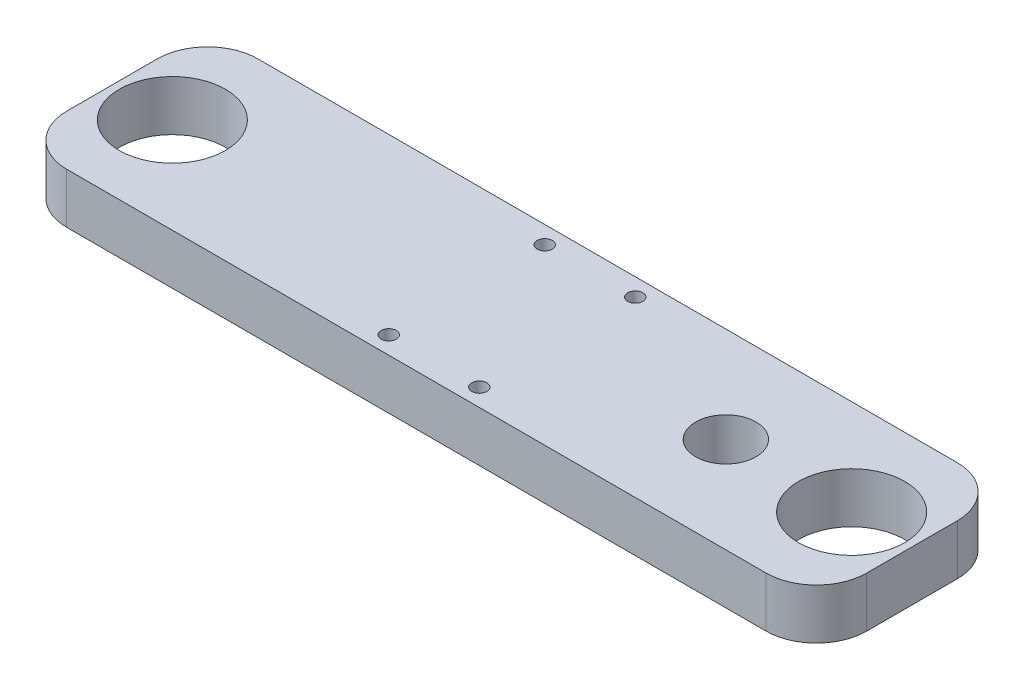
SolidWorks part; units mm, degrees
ref_plane "Front Plane" through (0, 0, 0) normal (0, 0, 1) x (1, 0, 0)
ref_plane "Top Plane" through (0, 0, 0) normal (0, 1, 0) x (1, 0, 0)
ref_plane "Right Plane" through (0, 0, 0) normal (1, 0, 0) x (0, 0, -1)
sketch "Sketch1" plane through (0, 0, 0) normal (0, 1, 0) x (1, 0, 0)
  line L0 (-67.5, 0) -> (67.5, 0) construction
  line L1 (-79.5, -19) -> (79.5, -19)
  line L2 (-79.5, -19) -> (-79.5, 19)
  line L3 (-79.5, 19) -> (79.5, 19)
  line L4 (79.5, -19) -> (79.5, 19)
  line L5 (-79.5, -19) -> (79.5, 19) construction
  line L6 (-79.5, 19) -> (79.5, -19) construction
  line L7 (-9, -15.5) -> (9, -15.5) construction
  line L8 (-9, -15.5) -> (-9, 15.5) construction
  line L9 (-9, 15.5) -> (9, 15.5) construction
  line L10 (9, -15.5) -> (9, 15.5) construction
  line L11 (-9, -15.5) -> (9, 15.5) construction
  line L12 (-9, 15.5) -> (9, -15.5) construction
  line L13 (0, -15.5) -> (0, 15.5) construction
  circle A1 centre (9, 15.5) radius 1.5
  circle A2 centre (-9, 15.5) radius 1.5
  circle A3 centre (-9, -15.5) radius 1.5
  circle A4 centre (9, -15.5) radius 1.5
  circle A5 centre (-67.5, 0) radius 10.55
  circle A6 centre (67.5, 0) radius 10.55
  circle A7 centre (42.5, 0) radius 6
  point P0 (0, 0)
  point P6 (0, 0)
  point P21 (0, 0)
  dimension "D3" = 12
  dimension "D5" = 3
  dimension "D7" = 21.1
  dimension "D8" = 25
  dimension "D1" = 159
  dimension "D2" = 38
  dimension "D4" = 18
  dimension "D6" = 135
extrude "Boss-Extrude1" add sketch "Sketch1" along normal blind 10
fillet "Fillet1" radius 10 4 edges at (79.5, 5, 19) (79.5, 5, -19) (-79.5, 5, -19) (-79.5, 5, 19)
